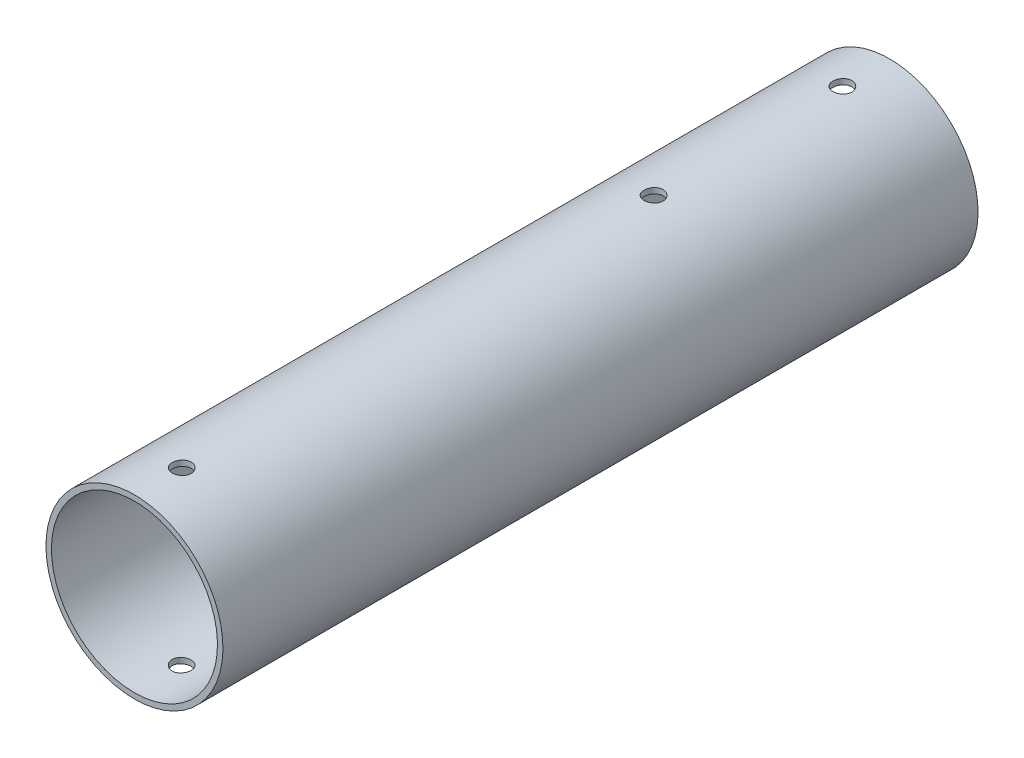
SolidWorks part; units mm, degrees
material "6061-T6 (SS)"
ref_plane "Front Plane" through (0, 0, 0) normal (0, 0, 1) x (1, 0, 0)
ref_plane "Top Plane" through (0, 0, 0) normal (0, 1, 0) x (1, 0, 0)
ref_plane "Right Plane" through (0, 0, 0) normal (1, 0, 0) x (0, 0, -1)
sketch "Sketch1" plane through (0, 0, 0) normal (0, 0, 1) x (1, 0, 0)
  line L0 (23.8125, 0) -> (22.3393, 0) construction
  circle A0 centre (0, 0) radius 23.8125
  circle A1 centre (0, 0) radius 22.3393
  point P4 (22.3393, 0)
  point P5 (23.8125, 0)
  point P6 (0, 23.8125)
  point P7 (0, 22.3393)
  dimension "OD" = 47.625
  dimension "ID" = 44.6786
  dimension "Wall Thickness" = 1.4732
sketch "Sketch2" plane through (0, 0, 0) normal (1, 0, 0) x (0, 0, -1)
  line L0 (-101.6, 0) -> (101.6, 0) construction
  line L2 (-101.6, 23.8125) -> (101.6, 23.8125) construction
  line L3 (-101.6, 23.8125) -> (-101.6, 22.3393) construction
  line L4 (-101.6, 22.3393) -> (101.6, 22.3393) construction
  line L5 (101.6, 23.8125) -> (101.6, 22.3393) construction
  line L7 (-6.35, 0) -> (6.35, 0) construction
  point P4 (0, 0)
  point P19 (0, 0)
  dimension "Length" = 203.2
sketch "Sketch3" plane through (0, 0, 0) normal (1, 0, 0) x (0, 0, -1)
  line L0 (-101.6, 0) -> (101.6, 0) construction
  line L1 (-101.6, 23.8125) -> (101.6, 23.8125)
  line L2 (-101.6, 23.8125) -> (-101.6, 22.3393)
  line L3 (-101.6, 22.3393) -> (101.6, 22.3393)
  line L4 (101.6, 23.8125) -> (101.6, 22.3393)
  line L5 (-101.6, 0) -> (101.6, 0) construction
revolve "Revolve1" add sketch "Sketch3" angle 360 about L5
sketch "Sketch4" plane through (0, 0, 0) normal (0, 1, 0) x (1, 0, 0)
  line L0 (0, 88.9) -> (0, 38.1) construction
  line L1 (23.8125, 101.6) -> (-23.8125, 101.6) construction
  line L2 (44.45, -101.6) -> (-44.45, -101.6) construction
  circle A0 centre (0, 88.9) radius 2.5527
  circle A1 centre (0, 38.1) radius 2.5527
  circle A2 centre (0, -88.9) radius 2.5527
  dimension "D1" = 5.1054
  dimension "D2" = 12.7
  dimension "D3" = 63.5
  dimension "D4" = 12.7
extrude "Cut-Extrude1" cut sketch "Sketch4" against normal through all both and the other way through all
sketch "Sketch5" plane through (0, 0, 0) normal (0, 1, 0) x (1, 0, 0)
  line L1 (9.525, -19.05) -> (-9.525, -19.05)
  line L2 (12.7, -15.875) -> (12.7, 15.875)
  line L3 (9.525, 19.05) -> (-9.525, 19.05)
  line L4 (-12.7, -15.875) -> (-12.7, 15.875)
  line L5 (12.7, -19.05) -> (-12.7, 19.05) construction
  line L6 (12.7, 19.05) -> (-12.7, -19.05) construction
  arc A0 (-9.525, -19.05) -> (-12.7, -15.875) centre (-9.525, -15.875) cw
  arc A1 (9.525, -19.05) -> (12.7, -15.875) centre (9.525, -15.875) ccw
  arc A2 (12.7, 15.875) -> (9.525, 19.05) centre (9.525, 15.875) ccw
  arc A3 (-9.525, 19.05) -> (-12.7, 15.875) centre (-9.525, 15.875) ccw
  point P0 (0, 0)
  dimension "D1" = 3.175
  dimension "D2" = 25.4
  dimension "D3" = 38.1
extrude "Cut-Extrude2" cut sketch "Sketch5" against normal through all
equation "\"ID@Sketch1\"=\"OD@Sketch1\"-(2*\"Wall Thickness@Sketch1\")"
